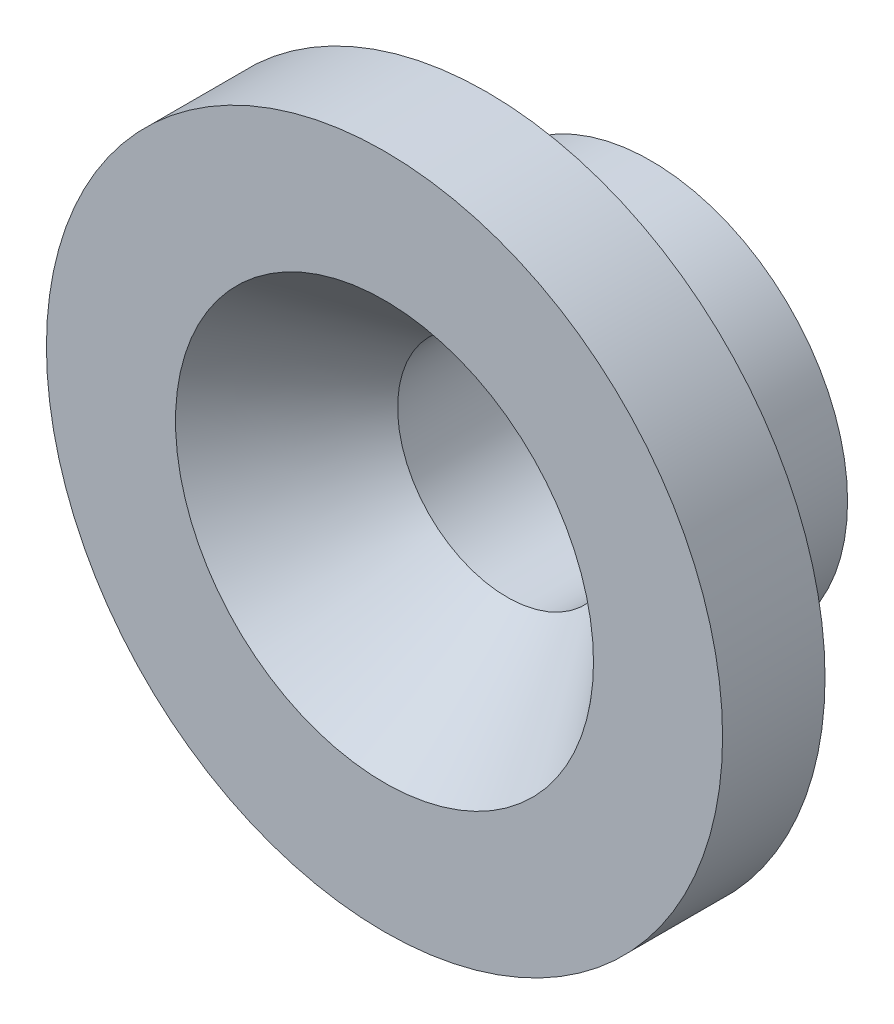
SolidWorks part; units mm, degrees
ref_plane "Front" through (0, 0, 0) normal (0, 0, 1) x (1, 0, 0)
ref_plane "Top" through (0, 0, 0) normal (0, 1, 0) x (1, 0, 0)
ref_plane "Right" through (0, 0, 0) normal (1, 0, 0) x (0, 0, -1)
sketch "Sketch1" plane through (0, 0, 0) normal (0, 0, 1) x (1, 0, 0)
  circle A0 centre (0, 0) radius 4.8
  dimension "D1" = 9.6
extrude "Boss-Extrude1" add sketch "Sketch1" along normal blind 4
sketch "Sketch2" plane through (0, 0, 4) normal (0, 0, 1) x (1, 0, 0)
  circle A0 centre (0, 0) radius 8.25
  dimension "D1" = 16.5
extrude "Boss-Extrude2" add sketch "Sketch2" along normal blind 2.5
sketch "Sketch3" plane through (0, 0, 6.5) normal (0, 0, 1) x (1, 0, 0)
  circle A0 centre (0, 0) radius 2.675
  dimension "D1" = 5.35
extrude "Cut-Extrude1" cut sketch "Sketch3" against normal up to surface (6.5 mm away) up to face at (4.8, 0, 0)
sketch "Sketch4" plane through (0, 0, 6.5) normal (0, 0, 1) x (1, 0, 0)
  circle A0 centre (0, 0) radius 5.1
  dimension "D1" = 10.2
extrude "Cut-Extrude2" cut sketch "Sketch4" against normal blind 3 draft 39
